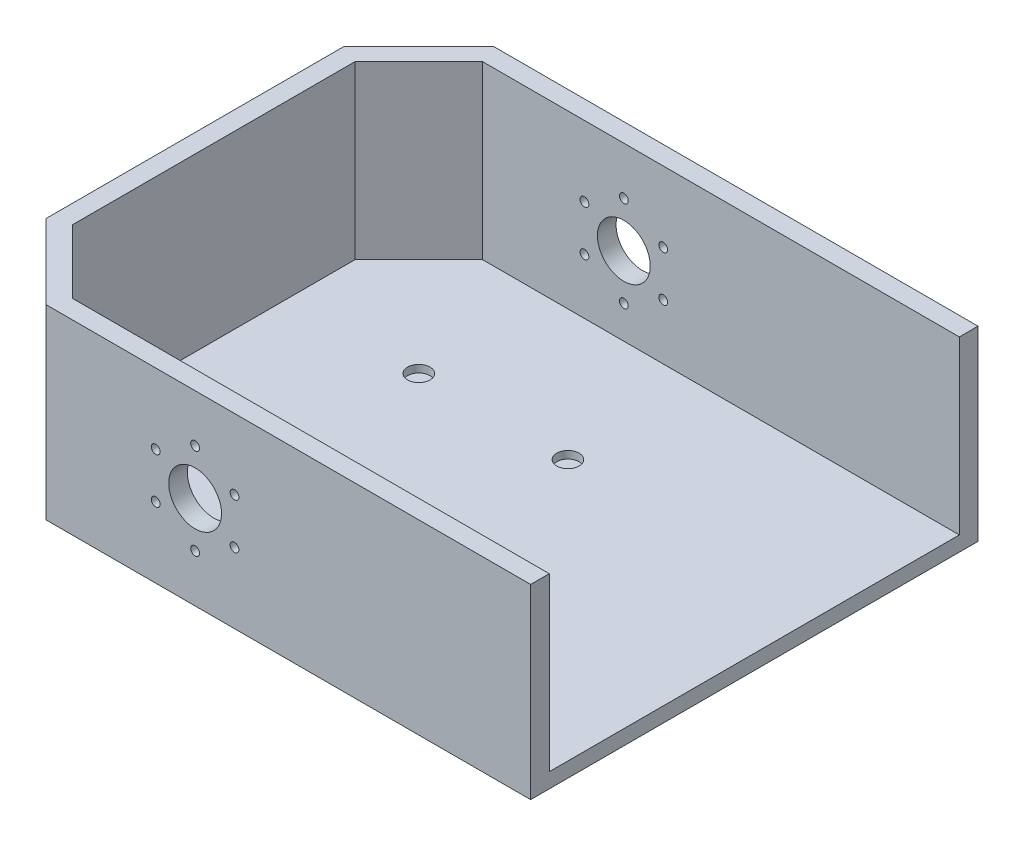
SolidWorks part; units mm, degrees
ref_plane "Front Plane" through (0, 0, 0) normal (0, 0, 1) x (1, 0, 0)
ref_plane "Top Plane" through (0, 0, 0) normal (0, 1, 0) x (1, 0, 0)
ref_plane "Right Plane" through (0, 0, 0) normal (1, 0, 0) x (0, 0, -1)
sketch "Sketch2" plane through (0, 0, 0) normal (0, 1, 0) x (1, 0, 0)
  line L1 (-127, 76.2) -> (63.5, 76.2)
  line L2 (-127, 76.2) -> (-127, -76.2)
  line L3 (-127, -76.2) -> (63.5, -76.2)
  line L4 (63.5, 76.2) -> (63.5, -76.2)
  dimension "D1" = 190.5
  dimension "D2" = 152.4
  dimension "D3" = 76.2
  dimension "D4" = 63.5
extrude "Boss-Extrude1" add sketch "Sketch2" along normal blind 5.08
chamfer "Chamfer1" distance 25.4 angle 45 2 edges at (-127, 2.54, -76.2) (-127, 2.54, 76.2)
sketch "Sketch4" plane through (0, 5.08, 0) normal (0, 1, 0) x (1, 0, 0)
  line L0 (57.15, 69.85) -> (-98.9697, 69.85)
  line L1 (-98.9697, 69.85) -> (-120.65, 48.1697)
  line L2 (-120.65, 48.1697) -> (-120.65, -48.1697)
  line L3 (-120.65, -48.1697) -> (-98.9697, -69.85)
  line L4 (-98.9697, -69.85) -> (57.15, -69.85)
  line L6 (63.5, 76.2) -> (-101.6, 76.2)
  line L7 (-101.6, 76.2) -> (-127, 50.8)
  line L8 (-127, 50.8) -> (-127, -50.8)
  line L9 (-127, -50.8) -> (-101.6, -76.2)
  line L10 (-101.6, -76.2) -> (63.5, -76.2)
  line L11 (63.5, -76.2) -> (63.5, 76.2)
  line L12 (63.5, 76.2) -> (-101.6, 76.2)
  line L13 (-101.6, 76.2) -> (-127, 50.8)
  line L14 (-127, 50.8) -> (-127, -50.8)
  line L15 (-127, -50.8) -> (-101.6, -76.2)
  line L16 (-101.6, -76.2) -> (63.5, -76.2)
  line L17 (63.5, -76.2) -> (63.5, -69.85)
  line L18 (57.15, 69.85) -> (63.5, 69.85)
  line L19 (57.15, -69.85) -> (63.5, -69.85)
  line L20 (63.5, 69.85) -> (63.5, 76.2)
  line L21 (63.5, -76.2) -> (63.5, 76.2) construction
  line L22 (57.15, -69.85) -> (57.15, 69.85) construction
  dimension "D2" = 6.35
  dimension "D1" = 0
extrude "Boss-Extrude3" add sketch "Sketch4" along normal blind 58.42
sketch "Sketch5" plane through (0, 0, 76.2) normal (0, 0, 1) x (1, 0, 0)
  line L0 (-150.3871, 38.1) -> (157.7429, 38.1) construction
  line L1 (-101.6, 0) -> (63.5, 0) construction
  line L2 (0, -14.9262) -> (0, 83.7522) construction
  line L3 (-50.8, 49.8289) -> (-50.8, 11.4994) construction
  line L5 (-71.0506, 31.75) -> (-33.7726, 31.75) construction
  circle A0 centre (-50.8, 31.75) radius 9
  circle A1 centre (-50.8, 31.75) radius 15.5 construction
  circle A2 centre (-50.8, 47.25) radius 1.5
  circle A3 centre (-37.3766, 39.5) radius 1.5
  circle A4 centre (-37.3766, 24) radius 1.5
  circle A5 centre (-50.8, 16.25) radius 1.5
  circle A6 centre (-64.2234, 24) radius 1.5
  circle A7 centre (-64.2234, 39.5) radius 1.5
  dimension "D2" = 18
  dimension "D5" = 31
  dimension "D6" = 3
  dimension "D1" = 38.1
  dimension "D3" = 50.8
  dimension "D4" = 6.35
  dimension "D7" = 6
extrude "Cut-Extrude1" cut sketch "Sketch5" against normal through all
sketch "Sketch7" plane through (0, 5.08, 0) normal (0, 1, 0) x (1, 0, 0)
  line L0 (33.4878, 0) -> (-147.4125, 0) construction
  line L1 (-76.2, 25.4) -> (-25.4, 25.4) construction
  line L2 (-76.2, 25.4) -> (-76.2, -25.4) construction
  line L3 (-76.2, -25.4) -> (-25.4, -25.4) construction
  line L4 (-25.4, 25.4) -> (-25.4, -25.4) construction
  line L5 (-50.8, 72.7262) -> (-50.8, -86.6673) construction
  circle A0 centre (-76.2, 25.4) radius 3.81
  circle A1 centre (-25.4, 25.4) radius 3.81
  circle A2 centre (-25.4, -25.4) radius 3.81
  circle A3 centre (-76.2, -25.4) radius 3.81
  dimension "D6" = 7.62
  dimension "D7" = 7.62
  dimension "D8" = 7.62
  dimension "D9" = 7.62
  dimension "D1" = 50.8
  dimension "D2" = 50.8
  dimension "D3" = 25.4
  dimension "D4" = 25.4
  dimension "D5" = 50.8
extrude "Cut-Extrude2" cut sketch "Sketch7" against normal blind 2.54 contours A0 | A1 | A2 | A3
